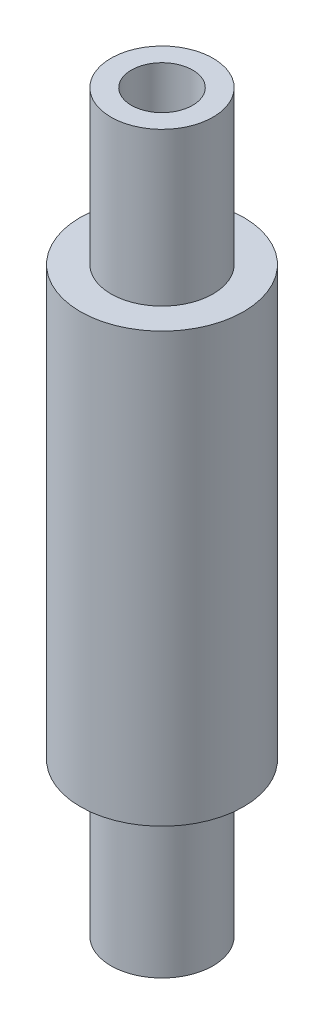
SolidWorks part; units mm, degrees
material "PET"
ref_plane "Front Plane" through (0, 0, 0) normal (0, 0, 1) x (1, 0, 0)
ref_plane "Top Plane" through (0, 0, 0) normal (0, 1, 0) x (1, 0, 0)
ref_plane "Right Plane" through (0, 0, 0) normal (1, 0, 0) x (0, 0, -1)
sketch "Sketch1" plane through (0, 0, 0) normal (0, 1, 0) x (1, 0, 0)
  circle A0 centre (0, 0) radius 4
  circle A1 centre (0, 0) radius 1.25
  dimension "D1" = 2.5
  dimension "D2" = 8
extrude "Boss-Extrude1" add sketch "Sketch1" along normal blind 21
sketch "Sketch2" plane through (0, 0, 0) normal (0, -1, 0) x (1, 0, 0)
  circle A0 centre (0, 0) radius 2.5
  dimension "D1" = 5
extrude "Boss-Extrude2" add sketch "Sketch2" along normal blind 7.5
sketch "Sketch3" plane through (0, 21, 0) normal (0, 1, 0) x (1, 0, 0)
  circle A0 centre (0, 0) radius 2.5
  dimension "D1" = 5
extrude "Boss-Extrude3" add sketch "Sketch3" along normal blind 7.5
sketch "Sketch4" plane through (0, 28.5, 0) normal (0, 1, 0) x (1, 0, 0)
  circle A0 centre (0, 0) radius 1.5
  dimension "D1" = 3
extrude "Cut-Extrude1" cut sketch "Sketch4" against normal through all
